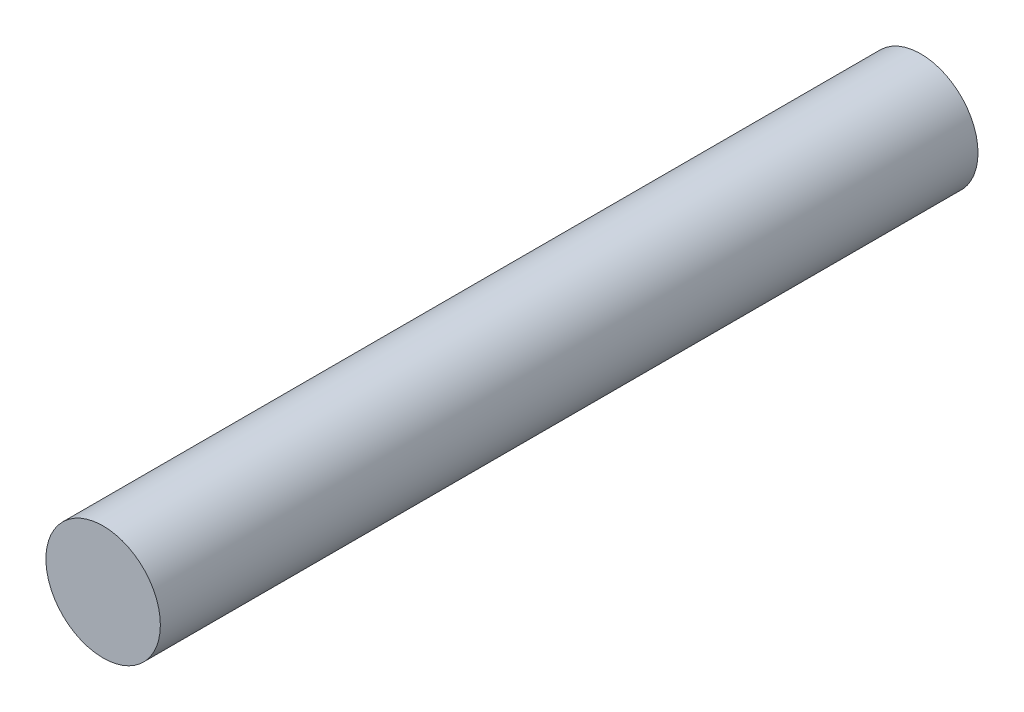
SolidWorks part; units mm, degrees
ref_plane "Спереди" through (0, 0, 0) normal (0, 0, 1) x (1, 0, 0)
ref_plane "Сверху" through (0, 0, 0) normal (0, 1, 0) x (1, 0, 0)
ref_plane "Справа" through (0, 0, 0) normal (1, 0, 0) x (0, 0, -1)
sketch "Эскиз1" plane through (0, 0, 0) normal (0, 0, 1) x (1, 0, 0)
  circle A0 centre (0, 0) radius 3.85
  dimension "D1" = 7.7
extrude "Бобышка-Вытянуть1" add sketch "Эскиз1" along normal blind 55
